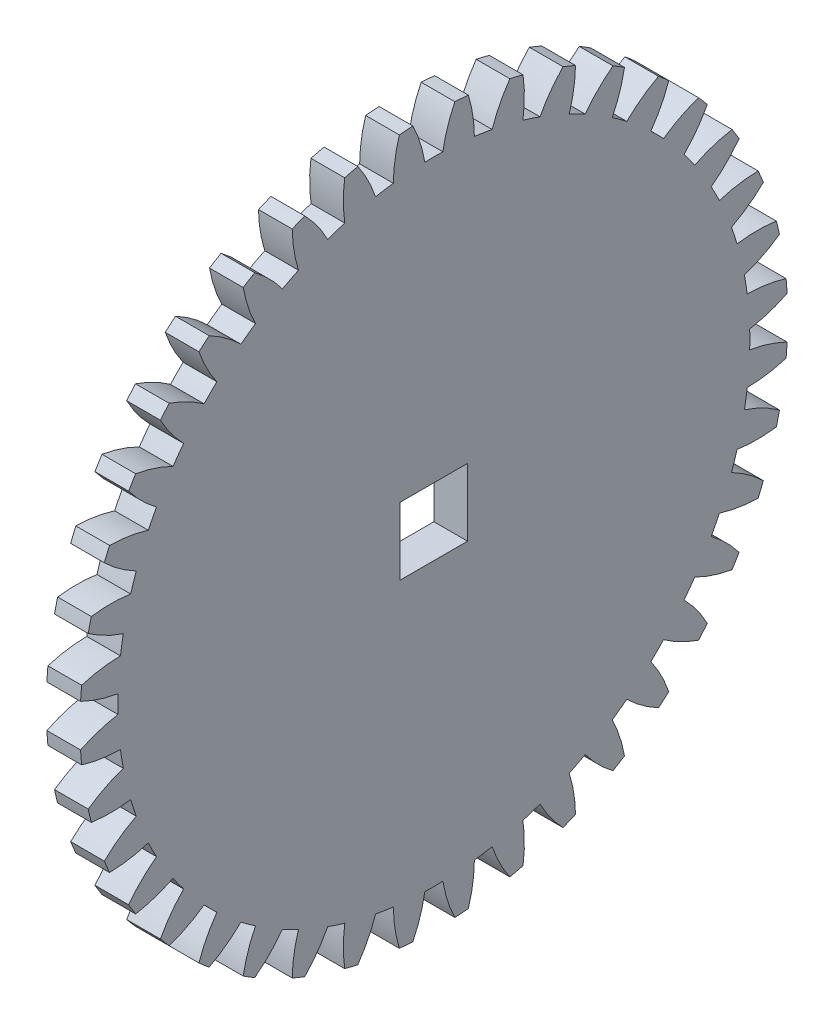
SolidWorks part; units mm, degrees
ref_plane "Plane1" through (0, 0, 0) normal (0, 0, 1) x (1, 0, 0)
ref_plane "Plane2" through (0, 0, 0) normal (0, 1, 0) x (1, 0, 0)
ref_plane "Plane3" through (0, 0, 0) normal (1, 0, 0) x (0, 0, -1)
other "Configuration Table"
sketch "HoldingSke" plane through (0, 0, 0) normal (0, 1, 0) x (1, 0, 0)
  line L0 (0, 0) -> (0.383, -0.3214)
  line L1 (-15, 0) -> (100, 0) construction
  line L2 (0, 0) -> (-2.1039, 2.3779)
  line L3 (0, 0) -> (-11.863, 4.5341)
  line L4 (0, 0) -> (6.6156, 5.5511)
  line L5 (0, 0) -> (-46.8476, -17.4728)
  line L6 (0, 0) -> (-3.3159, -2.2372)
  line L7 (-2.1039, 2.3779) -> (8.6587, 51.2062)
  line L8 (-76.2, 54.61) -> (-76.1, 54.61)
  line L9 (-67.7845, 28.3722) -> (-49.3413, 33.142)
  line L10 (-76.2, 71.12) -> (104.1128, 71.12)
  line L11 (0, 0) -> (-4, 0)
  line L12 (-76.2, 101.6) -> (-76.133, 101.6)
  line L13 (24.9733, 27.94) -> (52.9518, 28.4284)
  line L14 (24.9733, 27.94) -> (24.9743, 27.94)
  line L15 (24.9733, 27.94) -> (100.4006, 29.5858)
  line L16 (-63.627, -2) -> (-12.827, -2)
  circle A0 centre (0, 0) radius 0.4
  circle A1 centre (0, 0) radius 37.499
  circle A2 centre (0, 0) radius 37.5
  circle A3 centre (0, 0) radius 0.4
  dimension "MHD" = 74.998
  dimension "Hub_dia" = 75
  dimension "Bore" = 0.8
  dimension "MBD" = 0.8
  dimension "Num_teeth" = 40
  dimension "Pitch" = 0.5
  dimension "Overall_len" = 50
  dimension "Show_teeth" = 40
  dimension "Thickness" = 4
  dimension "OAL" = 50.0004
  dimension "T_dim" = 0.1
  dimension "Ap" = 14.5
  dimension "H" = 19.05
  dimension "Pitch_radius" = 180.3128
  dimension "Width" = 4
  dimension "Backlash" = 0.067
  dimension "Addendum_fac" = 1
  dimension "Dedendum_fac" = 1.25
  dimension "Clearance_fac" = 0.25
  dimension "Dedendum_add" = 0.001
  dimension "Module" = 2
sketch "BasProSke" plane through (0, 0, 0) normal (0, 1, 0) x (1, 0, 0)
  line L0 (-10, 0) -> (60, 0) construction
  line L1 (0, 0) -> (0, 42)
  line L2 (0, 0) -> (4, 0)
  line L3 (4, 0) -> (4, 42)
  line L4 (4, 42) -> (0, 42)
  dimension "Thickness" = 4
  dimension "Diameter" = 84
revolve "Base-Revolve" add sketch "BasProSke" angle 360 about L0
sketch "TooCutSke" plane through (0, 0, 0) normal (1, 0, 0) x (0, 0, -1)
  line L1 (0, 0) -> (0, 107) construction
  line L2 (0, 0) -> (-1.6876, 39.9644) construction
  line L3 (0, 0) -> (-6.2726, 79.7007) construction
  line L4 (-1.6876, 39.9644) -> (-3.1363, 39.8504) construction
  arc A0 (1.0692, 37.4838) -> (-1.0692, 37.4838) centre (0, 0) ccw
  arc A1 (2.5075, 41.9505) -> (-2.5075, 41.9505) centre (0, 0) ccw
  circle A2 centre (0, 0) radius 40 construction
  circle A3 centre (0, 0) radius 38.7259 construction
  arc A4 (-1.0692, 37.4838) -> (-2.5075, 41.9505) centre (-16.8537, 34.8662) ccw
  arc A5 (2.5075, 41.9505) -> (1.0692, 37.4838) centre (16.8537, 34.8662) ccw
  dimension "Root_dia" = 74.998
  dimension "Overcut_dia" = 84.0508
  dimension "Pitch_dia" = 80
  dimension "Base_dia" = 77.4518
  dimension "Flank_rad" = 16
  dimension "Half_ang" = 4.5
  dimension "Half_CT" = 1.4531
extrude "ToothCut" cut sketch "TooCutSke" along normal through all
fillet "Breaks" [suppressed] radius 0.04
fillet "RootFillets" [suppressed] radius 0.501
pattern_circular "TeethCuts" count 40 every 9 about axis through (-10, 0, 0) along (1, 0, 0) of "ToothCut", "RootFillets", "Breaks"
sketch "HubNeaOneSke" plane through (0, 0, 0) normal (-1, 0, 0) x (0, 0, 1)
  circle A0 centre (0, 0) radius 37.499
  dimension "Diameter" = 74.998
extrude "HubNearOne" [suppressed] add sketch "HubNeaOneSke" along normal blind 46.0004
sketch "HubNeaBotSke" plane through (0, 0, 0) normal (-1, 0, 0) x (0, 0, 1)
  circle A0 centre (0, 0) radius 37.499
  dimension "Diameter" = 74.998
extrude "HubNearBoth" [suppressed] add sketch "HubNeaBotSke" along normal blind 23.0002
ref_plane "FarPln" through (4, 0, 0) normal (1, 0, 0) x (0, 0, -1)
sketch "HubFarSke" plane through (4, 0, 0) normal (1, 0, 0) x (0, 0, -1)
  circle A0 centre (0, 0) radius 37.499
  dimension "Diameter" = 74.998
extrude "HubFar" [suppressed] add sketch "HubFarSke" along normal blind 23.0002
sketch "KeySke" plane through (0, 0, 0) normal (1, 0, 0) x (0, 0, -1)
  line L0 (-0.05, 0) -> (-0.05, 0.5)
  line L1 (-0.05, 0.5) -> (0.05, 0.5)
  line L2 (0.05, 0.5) -> (0.05, 0)
  line L3 (0, 0) -> (0, 34) construction
  line L4 (-0.05, 0) -> (0.05, 0)
  dimension "Offset" = 0.5
  dimension "Width" = 0.1
extrude "Keyway" [suppressed] cut sketch "KeySke" along normal mid plane 100.0007
pattern_circular "Keyway2" [suppressed] count 2 every 90 about axis through (-10, 0, 0) along (1, 0, 0)
sketch "草图1" plane through (4, 0, 0) normal (1, 0, 0) x (0, 0, -1)
  line L1 (-4, 4) -> (4, 4)
  line L2 (-4, 4) -> (-4, -4)
  line L3 (-4, -4) -> (4, -4)
  line L4 (4, 4) -> (4, -4)
  line L5 (-4, 4) -> (4, -4) construction
  line L6 (-4, -4) -> (4, 4) construction
  point P0 (0, 0)
  dimension "D1" = 8
  dimension "D2" = 8
extrude "切除-拉伸1" cut sketch "草图1" against normal through all
equation "' \"Module@HoldingSke\" = 6.35"
equation "' \"Num_teeth@HoldingSke\" = 12"
equation "' \"Ap@HoldingSke\" =  20"
equation "' \"Ap@HoldingSke\" = 20"
equation "' \"Width@HoldingSke\" = 0.5 * 25.4"
equation "' \"Hub_dia@HoldingSke\"= 1 * 25.4"
equation "' \"Hub_dia@HoldingSke\" = 1 * 25.4"
equation "' \"Overall_len@HoldingSke\" = 1.0 * 25.4"
equation "' \"Bore@HoldingSke\" = 0.75 * 25.4"
equation "' \"T_dim@HoldingSke\" = 0.1 * 25.4"
equation "' \"Width@KeySke\" = 0.25 * 25.4"
equation "' \"Show_teeth@HoldingSke\" = 13"
equation "' \"Backlash@HoldingSke\" = 0.009 * 25.4"
equation "' \"Addendum_fac@HoldingSke\" = 1.0"
equation "' \"Dedendum_fac@HoldingSke\" = 1.25"
equation "' \"Dedendum_add@HoldingSke\" = 0.00005 * 25.4"
equation "' \"Clearance_fac@HoldingSke\" = 0.25"
equation "\"Pitch@HoldingSke\" = 1 / \"Module@HoldingSke\""
equation "\"Overcut_dia@TooCutSke\" = (\"Num_teeth@HoldingSke\" + 2 * \"Addendum_fac@HoldingSke\") / \"Pitch@HoldingSke\" + 0.002 * 25.4"
equation "\"Pitch_dia@TooCutSke\" = \"Num_teeth@HoldingSke\" / \"Pitch@HoldingSke\""
equation "\"Base_dia@TooCutSke\" = \"Num_teeth@HoldingSke\" / \"Pitch@HoldingSke\" * cos((\"Ap@HoldingSke\"  * 3.14159265 / 180))"
equation "\"Root_dia@TooCutSke\" = (\"Num_teeth@HoldingSke\" + 2) / \"Pitch@HoldingSke\" - 2 * (\"Addendum_fac@HoldingSke\" + \"Dedendum_fac@HoldingSke\") / \"Pitch@HoldingSke\" - \"Dedendum_add@HoldingSke\" * 2"
equation "\"Half_ang@TooCutSke\" = 180 / \"Num_teeth@HoldingSke\""
equation "\"Half_CT@TooCutSke\" = \"Num_teeth@HoldingSke\" / \"Pitch@HoldingSke\" * sin((3.14159265 / 2 / \"Num_teeth@HoldingSke\")) / 2 - 7 * \"Backlash@HoldingSke\" / 4"
equation "\"Flank_rad@TooCutSke\" = \"Num_teeth@HoldingSke\" / \"Pitch@HoldingSke\" / 5"
equation "\"Radius@RootFillets\" = \"Clearance_fac@HoldingSke\" / \"Pitch@HoldingSke\" + \"Dedendum_add@HoldingSke\""
equation "\"Break_rad@Breaks\" = 0.02 / \"Pitch@HoldingSke\""
equation "\"Thickness@HoldingSke\" = \"Width@HoldingSke\""
equation "\"OAL@HoldingSke\" = \"Thickness@HoldingSke\""
equation "\"MHD@HoldingSke\" = (\"Num_teeth@HoldingSke\" + 2) / \"Pitch@HoldingSke\" - 2 * (\"Addendum_fac@HoldingSke\" + \"Dedendum_fac@HoldingSke\")  / \"Pitch@HoldingSke\" - \"Dedendum_add@HoldingSke\" * 2"
equation "\"MBD@HoldingSke\" = (\"Num_teeth@HoldingSke\" + 2) / \"Pitch@HoldingSke\" - 2 * (\"Addendum_fac@HoldingSke\" + \"Dedendum_fac@HoldingSke\")  / \"Pitch@HoldingSke\" - \"Dedendum_add@HoldingSke\" * 2 - 0.002 * 25.4"
equation "\"MHD@HoldingSke\" = ((sgn( \"MHD@HoldingSke\" - \"Hub_dia@HoldingSke\" )-1)*( \"MHD@HoldingSke\" - \"Hub_dia@HoldingSke\" ))/-2+ \"Hub_dia@HoldingSke\""
equation "\"MBD@HoldingSke\" = ((sgn( \"MBD@HoldingSke\" - \"Bore@HoldingSke\" )-1)*( \"MBD@HoldingSke\" - \"Bore@HoldingSke\" ))/-2+ \"Bore@HoldingSke\""
equation "\"OAL@HoldingSke\" = ((sgn( \"OAL@HoldingSke\" - \"Overall_len@HoldingSke\" )+1)*( \"OAL@HoldingSke\" - \"Overall_len@HoldingSke\" ))/2 + \"Overall_len@HoldingSke\" + 0.000002 * 25.4"
equation "\"Num_teeth@TeethCuts\" = int( \"Show_teeth@HoldingSke\" ) + 1"
equation "\"Num_teeth@TeethCuts\" = ((sgn( \"Num_teeth@TeethCuts\" - \"Num_teeth@HoldingSke\" )-1)*( \"Num_teeth@TeethCuts\" - \"Num_teeth@HoldingSke\" ))/-2+ \"Num_teeth@HoldingSke\""
equation "\"Num_teeth@TeethCuts\" = ((sgn( \"Num_teeth@TeethCuts\" - 2.0)+1)*( \"Num_teeth@TeethCuts\" - 2.0))/2 +2.0"
equation "\"Angle@TeethCuts\" = 360.0 / \"Num_teeth@HoldingSke\""
equation "\"Diameter@BasProSke\" = (\"Num_teeth@HoldingSke\" + 2 * \"Addendum_fac@HoldingSke\") / \"Pitch@HoldingSke\""
equation "\"Thickness@BasProSke\"  = \"Thickness@HoldingSke\""
equation "' \"Fillet_rad@BasProSke\" =  \"Thickness@HoldingSke\" * 0.05"
equation "' \"Fillet_rad@BasProSke\" = \"Thickness@HoldingSke\" * 0.05"
equation "\"MHD@HoldingSke\" = ((sgn( \"MHD@HoldingSke\" - \"Root_dia@TooCutSke\" )-1)*( \"MHD@HoldingSke\" - \"Root_dia@TooCutSke\" ))/-2+ \"Root_dia@TooCutSke\""
equation "\"Diameter@HubNeaOneSke\" = \"MHD@HoldingSke\""
equation "\"Length@HubNearOne\" = \"OAL@HoldingSke\" - \"Thickness@BasProSke\""
equation "\"Diameter@HubNeaBotSke\" = \"MHD@HoldingSke\""
equation "\"Length@HubNearBoth\" = ( \"OAL@HoldingSke\" - \"Thickness@BasProSke\" ) / 2.0"
equation "\"Thickness@FarPln\" = \"Thickness@BasProSke\""
equation "\"Diameter@HubFarSke\" = \"MHD@HoldingSke\""
equation "\"Length@HubFar\" = ( \"OAL@HoldingSke\" - \"Thickness@BasProSke\" ) / 2.0"
equation "\"D1@Keyway\" = \"OAL@HoldingSke\" * 2.0"
equation "\"Offset@KeySke\" = \"T_dim@HoldingSke\" + \"MBD@HoldingSke\" / 2.0"
